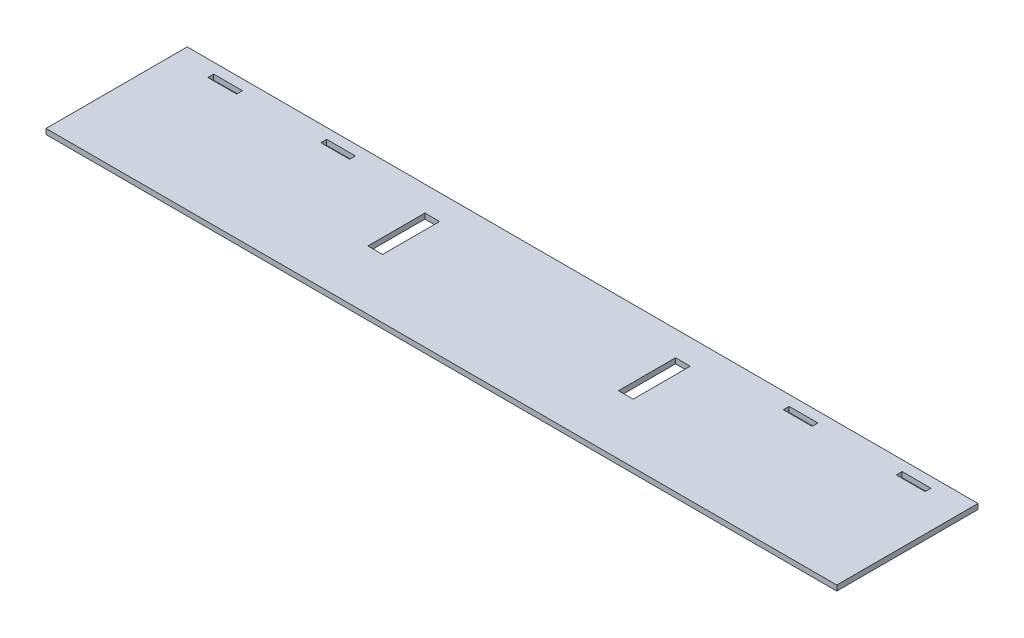
SolidWorks part; units mm, degrees
material "Plain Carbon Steel"
ref_plane "Front Plane" through (0, 0, 0) normal (0, 0, 1) x (1, 0, 0)
ref_plane "Top Plane" through (0, 0, 0) normal (0, 1, 0) x (1, 0, 0)
ref_plane "Right Plane" through (0, 0, 0) normal (1, 0, 0) x (0, 0, -1)
sketch "Sketch1" plane through (0, 0, 0) normal (0, 1, 0) x (1, 0, 0)
  line L1 (-355.6, 0) -> (355.6, 0)
  line L2 (-355.6, 0) -> (-355.6, 127)
  line L3 (-355.6, 127) -> (355.6, 127)
  line L4 (355.6, 0) -> (355.6, 127)
  dimension "D1" = 711.2
  dimension "D2" = 127
extrude "Boss-Extrude1" add sketch "Sketch1" along normal blind 4.7625
sketch "Sketch2" plane through (0, 0, 0) normal (0, -1, 0) x (-1, 0, 0)
  line L0 (-106.1085, 104.4839) -> (-106.1085, 53.1759)
  line L1 (119.0625, 104.2299) -> (106.3625, 104.2299)
  line L2 (119.0625, 104.2299) -> (119.0625, 53.4299)
  line L3 (119.0625, 53.4299) -> (106.3625, 53.4299)
  line L4 (106.3625, 104.2299) -> (106.3625, 53.4299)
  line L5 (-106.3625, 104.2299) -> (-119.0625, 104.2299)
  line L6 (-106.3625, 104.2299) -> (-106.3625, 53.4299)
  line L7 (-106.3625, 53.4299) -> (-119.0625, 53.4299)
  line L8 (-119.0625, 104.2299) -> (-119.0625, 53.4299)
  line L9 (-106.1085, 53.1759) -> (-119.3165, 53.1759)
  line L10 (-119.3165, 104.4839) -> (-119.3165, 53.1759)
  line L11 (-106.1085, 104.4839) -> (-119.3165, 104.4839)
  line L12 (119.3165, 104.4839) -> (106.1085, 104.4839)
  line L13 (106.1085, 104.4839) -> (106.1085, 53.1759)
  line L14 (119.3165, 53.1759) -> (106.1085, 53.1759)
  line L15 (119.3165, 104.4839) -> (119.3165, 53.1759)
  dimension "D1" = 0.254
extrude "Cut-Extrude1" cut sketch "Sketch2" against normal through all
sketch "Sketch3" plane through (0, 0, 0) normal (0, -1, 0) x (1, 0, 0)
  line L0 (-322.5165, -112.4585) -> (-296.6085, -112.4585)
  line L1 (-322.2625, -117.475) -> (-296.8625, -117.475)
  line L2 (-322.2625, -117.475) -> (-322.2625, -112.7125)
  line L3 (-322.2625, -112.7125) -> (-296.8625, -112.7125)
  line L4 (-296.8625, -117.475) -> (-296.8625, -112.7125)
  line L5 (-220.6625, -117.475) -> (-195.2625, -117.475)
  line L6 (-220.6625, -117.475) -> (-220.6625, -112.7125)
  line L7 (-220.6625, -112.7125) -> (-195.2625, -112.7125)
  line L8 (-195.2625, -117.475) -> (-195.2625, -112.7125)
  line L9 (195.2625, -112.7125) -> (220.6625, -112.7125)
  line L10 (195.2625, -112.7125) -> (195.2625, -117.475)
  line L11 (195.2625, -117.475) -> (220.6625, -117.475)
  line L12 (220.6625, -112.7125) -> (220.6625, -117.475)
  line L13 (296.8625, -112.7125) -> (322.2625, -112.7125)
  line L14 (296.8625, -112.7125) -> (296.8625, -117.475)
  line L15 (296.8625, -117.475) -> (322.2625, -117.475)
  line L16 (322.2625, -112.7125) -> (322.2625, -117.475)
  line L17 (-296.6085, -117.729) -> (-296.6085, -112.4585)
  line L18 (-322.5165, -117.729) -> (-296.6085, -117.729)
  line L19 (-322.5165, -117.729) -> (-322.5165, -112.4585)
  line L20 (-220.9165, -112.4585) -> (-195.0085, -112.4585)
  line L21 (-195.0085, -117.729) -> (-195.0085, -112.4585)
  line L22 (-220.9165, -117.729) -> (-195.0085, -117.729)
  line L23 (-220.9165, -117.729) -> (-220.9165, -112.4585)
  line L24 (195.0085, -112.4585) -> (220.9165, -112.4585)
  line L25 (220.9165, -112.4585) -> (220.9165, -117.729)
  line L26 (195.0085, -117.729) -> (220.9165, -117.729)
  line L27 (195.0085, -112.4585) -> (195.0085, -117.729)
  line L28 (296.6085, -112.4585) -> (322.5165, -112.4585)
  line L29 (322.5165, -112.4585) -> (322.5165, -117.729)
  line L30 (296.6085, -117.729) -> (322.5165, -117.729)
  line L31 (296.6085, -112.4585) -> (296.6085, -117.729)
  dimension "D1" = 0.254
extrude "Cut-Extrude2" cut sketch "Sketch3" against normal through all
